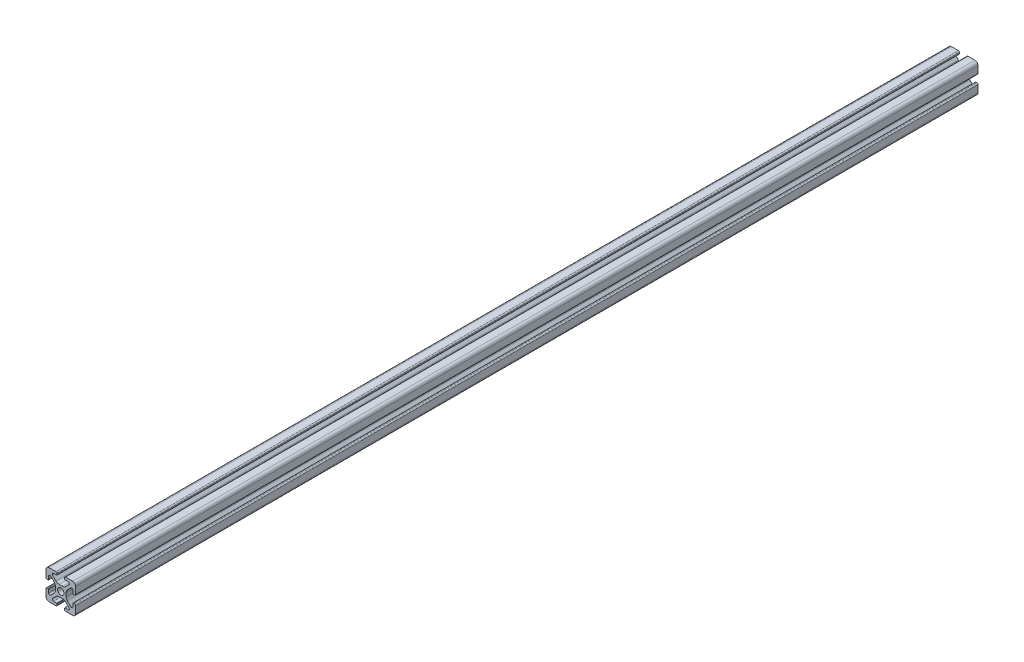
SolidWorks part; units mm, degrees
ref_plane "Front Plane" through (0, 0, 0) normal (0, 0, 1) x (1, 0, 0)
ref_plane "Top Plane" through (0, 0, 0) normal (0, 1, 0) x (1, 0, 0)
ref_plane "Right Plane" through (0, 0, 0) normal (1, 0, 0) x (0, 0, -1)
sketch "Sketch1" plane through (0, 0, 0) normal (0, 0, 1) x (1, 0, 0)
  line L0 (0, 9.9949) -> (0, -9.9949) construction
  line L1 (-9.9949, 0) -> (9.9949, 0) construction
  line L2 (-9.9949, 7.9883) -> (-9.9949, 3.2893)
  line L3 (-7.9883, 9.9949) -> (-3.2893, 9.9949)
  line L4 (-2.5019, 9.2075) -> (-2.5019, 8.4963)
  line L5 (-2.8067, 8.1915) -> (-4.9149, 8.1915)
  line L6 (-5.5076, 6.7606) -> (-3.2528, 4.5058)
  line L7 (-6.7606, 5.5076) -> (-4.5058, 3.2528)
  line L8 (-8.1915, 4.9149) -> (-8.1915, 2.8067)
  line L9 (-8.4963, 2.5019) -> (-9.2075, 2.5019)
  line L10 (0, 0) -> (-9.9949, 9.9949) construction
  line L11 (-1.1334, 3.6279) -> (1.1334, 3.6279)
  line L12 (-3.6279, 1.1334) -> (-3.6279, -1.1334)
  line L13 (8.4963, 2.5019) -> (9.2075, 2.5019)
  line L14 (8.1915, 4.9149) -> (8.1915, 2.8067)
  line L15 (9.9949, 7.9883) -> (9.9949, 3.2893)
  line L16 (7.9883, 9.9949) -> (3.2893, 9.9949)
  line L17 (2.5019, 9.2075) -> (2.5019, 8.4963)
  line L18 (2.8067, 8.1915) -> (4.9149, 8.1915)
  line L19 (3.6279, 1.1334) -> (3.6279, -1.1334)
  line L20 (5.5076, 6.7606) -> (3.2528, 4.5058)
  line L21 (6.7606, 5.5076) -> (4.5058, 3.2528)
  line L22 (-8.4963, -2.5019) -> (-9.2075, -2.5019)
  line L23 (-8.1915, -4.9149) -> (-8.1915, -2.8067)
  line L24 (-6.7606, -5.5076) -> (-4.5058, -3.2528)
  line L25 (-5.5076, -6.7606) -> (-3.2528, -4.5058)
  line L26 (-2.8067, -8.1915) -> (-4.9149, -8.1915)
  line L27 (-2.5019, -9.2075) -> (-2.5019, -8.4963)
  line L28 (-7.9883, -9.9949) -> (-3.2893, -9.9949)
  line L29 (-9.9949, -7.9883) -> (-9.9949, -3.2893)
  line L30 (9.9949, -7.9883) -> (9.9949, -3.2893)
  line L31 (7.9883, -9.9949) -> (3.2893, -9.9949)
  line L32 (2.5019, -9.2075) -> (2.5019, -8.4963)
  line L33 (2.8067, -8.1915) -> (4.9149, -8.1915)
  line L34 (5.5076, -6.7606) -> (3.2528, -4.5058)
  line L35 (6.7606, -5.5076) -> (4.5058, -3.2528)
  line L36 (8.1915, -4.9149) -> (8.1915, -2.8067)
  line L37 (8.4963, -2.5019) -> (9.2075, -2.5019)
  line L38 (-1.1334, -3.6279) -> (1.1334, -3.6279)
  circle A0 centre (0, 0) radius 2.1463
  arc A1 (-9.9949, 7.9883) -> (-7.9883, 9.9949) centre (-7.9883, 7.9883) cw
  arc A2 (-6.7606, 5.5076) -> (-8.1915, 4.9149) centre (-7.3533, 4.9149) ccw
  arc A3 (-4.9149, 8.1915) -> (-5.5076, 6.7606) centre (-4.9149, 7.3533) ccw
  arc A4 (-3.2893, 9.9949) -> (-2.5019, 9.2075) centre (-3.2893, 9.2075) cw
  arc A5 (-9.9949, 3.2893) -> (-9.2075, 2.5019) centre (-9.2075, 3.2893) ccw
  arc A6 (-8.1915, 2.8067) -> (-8.4963, 2.5019) centre (-8.4963, 2.8067) cw
  arc A7 (-2.5019, 8.4963) -> (-2.8067, 8.1915) centre (-2.8067, 8.4963) cw
  arc A8 (-1.1334, 3.6279) -> (-3.2528, 4.5058) centre (-1.1334, 6.6251) cw
  arc A9 (-3.6279, 1.1334) -> (-4.5058, 3.2528) centre (-6.6251, 1.1334) ccw
  arc A10 (8.1915, 2.8067) -> (8.4963, 2.5019) centre (8.4963, 2.8067) ccw
  arc A11 (9.9949, 3.2893) -> (9.2075, 2.5019) centre (9.2075, 3.2893) cw
  arc A12 (9.9949, 7.9883) -> (7.9883, 9.9949) centre (7.9883, 7.9883) ccw
  arc A13 (3.2893, 9.9949) -> (2.5019, 9.2075) centre (3.2893, 9.2075) ccw
  arc A14 (2.5019, 8.4963) -> (2.8067, 8.1915) centre (2.8067, 8.4963) ccw
  arc A15 (1.1334, 3.6279) -> (3.2528, 4.5058) centre (1.1334, 6.6251) ccw
  arc A16 (3.6279, 1.1334) -> (4.5058, 3.2528) centre (6.6251, 1.1334) cw
  arc A17 (6.7606, 5.5076) -> (8.1915, 4.9149) centre (7.3533, 4.9149) cw
  arc A18 (4.9149, 8.1915) -> (5.5076, 6.7606) centre (4.9149, 7.3533) cw
  arc A19 (-3.6279, -1.1334) -> (-4.5058, -3.2528) centre (-6.6251, -1.1334) cw
  arc A20 (-1.1334, -3.6279) -> (-3.2528, -4.5058) centre (-1.1334, -6.6251) ccw
  arc A21 (-2.5019, -8.4963) -> (-2.8067, -8.1915) centre (-2.8067, -8.4963) ccw
  arc A22 (-8.1915, -2.8067) -> (-8.4963, -2.5019) centre (-8.4963, -2.8067) ccw
  arc A23 (-9.9949, -3.2893) -> (-9.2075, -2.5019) centre (-9.2075, -3.2893) cw
  arc A24 (-3.2893, -9.9949) -> (-2.5019, -9.2075) centre (-3.2893, -9.2075) ccw
  arc A25 (-4.9149, -8.1915) -> (-5.5076, -6.7606) centre (-4.9149, -7.3533) cw
  arc A26 (-6.7606, -5.5076) -> (-8.1915, -4.9149) centre (-7.3533, -4.9149) cw
  arc A27 (-9.9949, -7.9883) -> (-7.9883, -9.9949) centre (-7.9883, -7.9883) ccw
  arc A28 (9.9949, -7.9883) -> (7.9883, -9.9949) centre (7.9883, -7.9883) cw
  arc A29 (6.7606, -5.5076) -> (8.1915, -4.9149) centre (7.3533, -4.9149) ccw
  arc A30 (4.9149, -8.1915) -> (5.5076, -6.7606) centre (4.9149, -7.3533) ccw
  arc A31 (3.2893, -9.9949) -> (2.5019, -9.2075) centre (3.2893, -9.2075) cw
  arc A32 (9.9949, -3.2893) -> (9.2075, -2.5019) centre (9.2075, -3.2893) ccw
  arc A33 (8.1915, -2.8067) -> (8.4963, -2.5019) centre (8.4963, -2.8067) cw
  arc A34 (2.5019, -8.4963) -> (2.8067, -8.1915) centre (2.8067, -8.4963) cw
  arc A35 (1.1334, -3.6279) -> (3.2528, -4.5058) centre (1.1334, -6.6251) cw
  arc A36 (3.6279, -1.1334) -> (4.5058, -3.2528) centre (6.6251, -1.1334) ccw
  point P29 (-9.9949, 2.5019)
  point P32 (-8.1915, 2.5019)
  point P36 (-2.3749, 3.6279)
  point P68 (0, 3.6279)
  dimension "D4" = 4.2926
  dimension "D5" = 2.0066
  dimension "D6" = 0.8382
  dimension "D9" = 0.7874
  dimension "D10" = 0.3048
  dimension "D13" = 2.9972
  dimension "D1" = 19.9898
  dimension "D2" = 19.9898
  dimension "D7" = 7.493
  dimension "D8" = 1.8034
  dimension "D12" = 11.5062
  dimension "D11" = 4.7498
extrude "Extrude1" add sketch "Sketch1" along normal mid plane 609.6
equation "\"D2@Sketch1\" = \"D1@Sketch1\""
